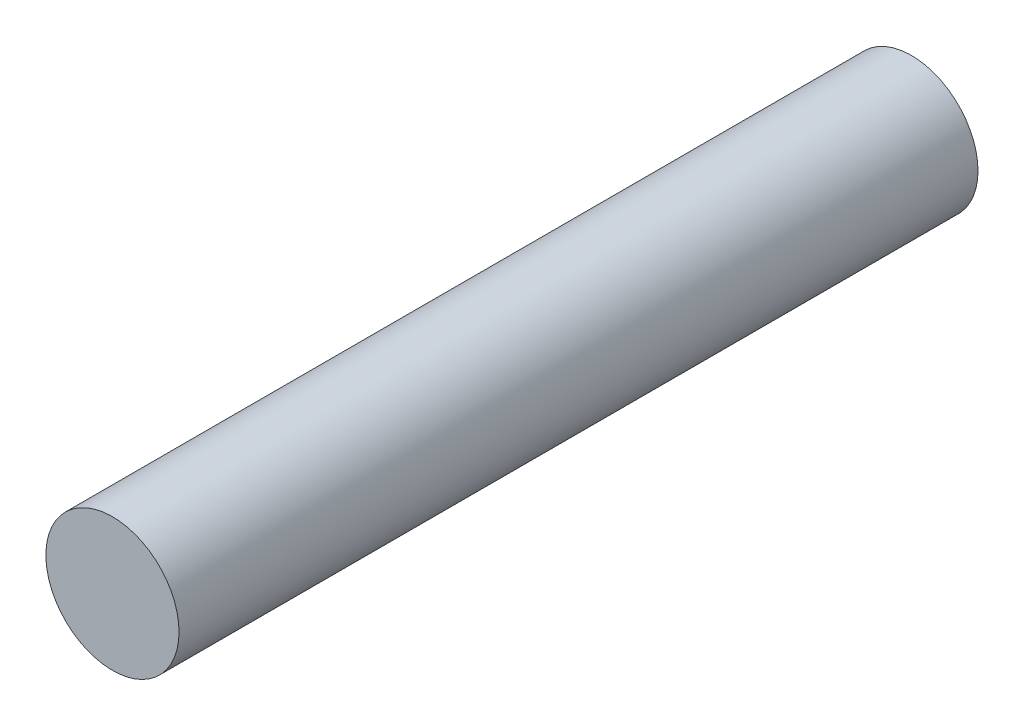
SolidWorks part; units mm, degrees
ref_plane "Front" through (0, 0, 0) normal (0, 0, 1) x (1, 0, 0)
ref_plane "Top" through (0, 0, 0) normal (0, 1, 0) x (1, 0, 0)
ref_plane "Right" through (0, 0, 0) normal (1, 0, 0) x (0, 0, -1)
sketch "Sketch1" plane through (0, 0, 0) normal (0, 0, 1) x (1, 0, 0)
  circle A0 centre (0, 0) radius 3.175
  dimension "D1" = 6.35
extrude "Boss-Extrude1" add sketch "Sketch1" along normal blind 38.1
